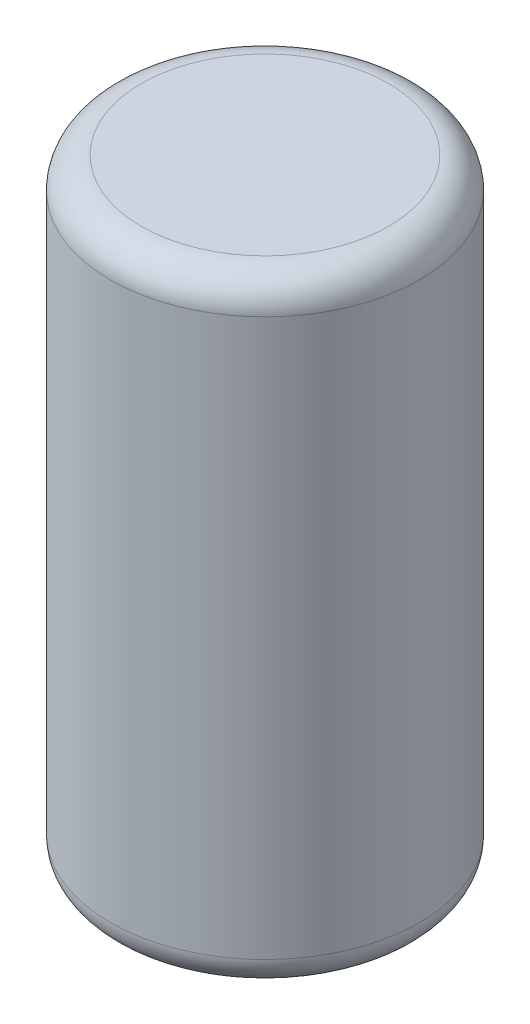
SolidWorks part; units mm, degrees
material "Alloy Steel"
ref_plane "Front Plane" through (0, 0, 0) normal (0, 0, 1) x (1, 0, 0)
ref_plane "Top Plane" through (0, 0, 0) normal (0, 1, 0) x (1, 0, 0)
ref_plane "Right Plane" through (0, 0, 0) normal (1, 0, 0) x (0, 0, -1)
sketch "Sketch1" plane through (0, 0, 0) normal (0, 1, 0) x (1, 0, 0)
  circle A0 centre (0, 0) radius 3.175
  dimension "D1" = 6.35
extrude "Boss-Extrude1" add sketch "Sketch1" along normal blind 12.7
fillet "Fillet1" radius 0.635 2 edges at (0, 0, 3.175) (0, 12.7, 3.175)
